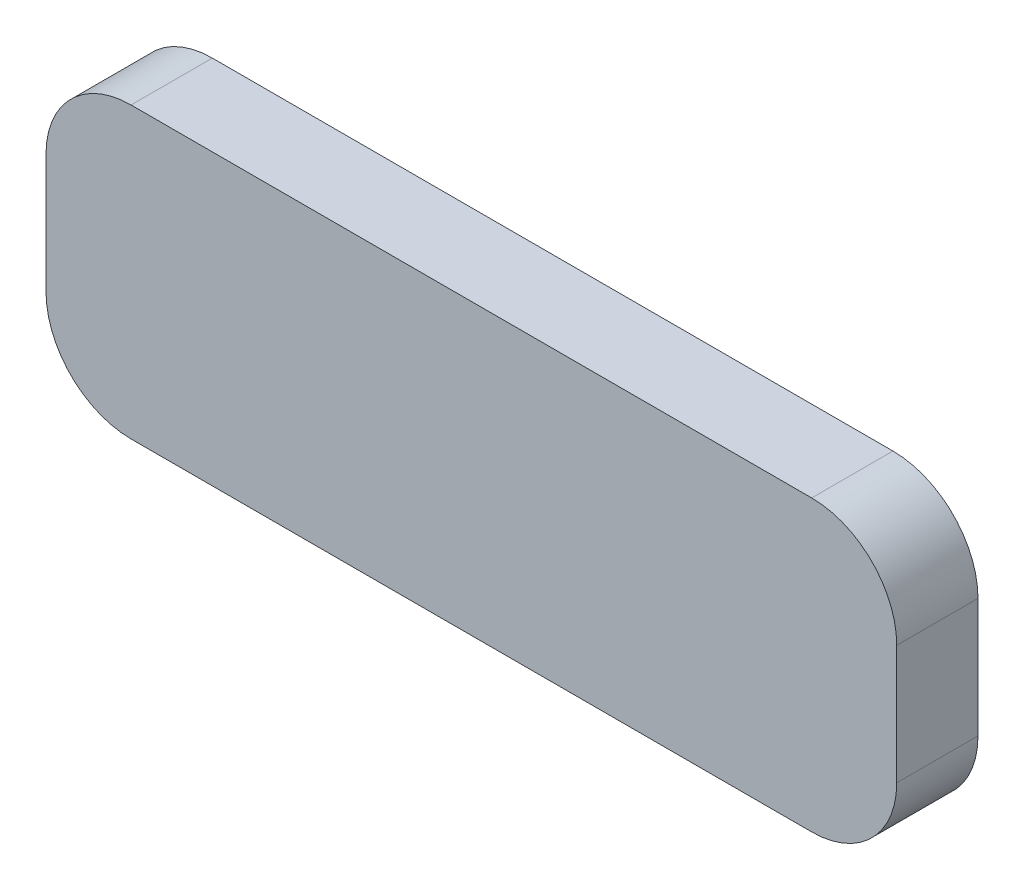
SolidWorks part; units mm, degrees
ref_plane "Front Plane" through (0, 0, 0) normal (0, 0, 1) x (1, 0, 0)
ref_plane "Top Plane" through (0, 0, 0) normal (0, 1, 0) x (1, 0, 0)
ref_plane "Right Plane" through (0, 0, 0) normal (1, 0, 0) x (0, 0, -1)
sketch "Sketch1" plane through (0, 0, 0) normal (0, 0, 1) x (1, 0, 0)
  line L0 (0, 0) -> (50, 0) construction
  line L1 (0, 0) -> (0, -4.7752) construction
  line L2 (5, -4.7752) -> (45, -4.7752)
  line L3 (50, -4.7752) -> (50, 0) construction
  line L4 (0, 0.2248) -> (0, 7.2248)
  line L5 (5, 12.2248) -> (45, 12.2248)
  line L6 (50, 7.2248) -> (50, 0.2248)
  arc A0 (0, 0.2248) -> (5, -4.7752) centre (5, 0.2248) ccw
  arc A1 (45, -4.7752) -> (50, 0.2248) centre (45, 0.2248) ccw
  arc A2 (45, 12.2248) -> (50, 7.2248) centre (45, 7.2248) cw
  arc A3 (0, 7.2248) -> (5, 12.2248) centre (5, 7.2248) cw
  point P17 (0, 12.2248)
  dimension "D4" = 5
  dimension "D1" = 50
  dimension "D2" = 4.7752
  dimension "D3" = 17
extrude "Boss-Extrude1" add sketch "Sketch1" along normal blind 4.7752
